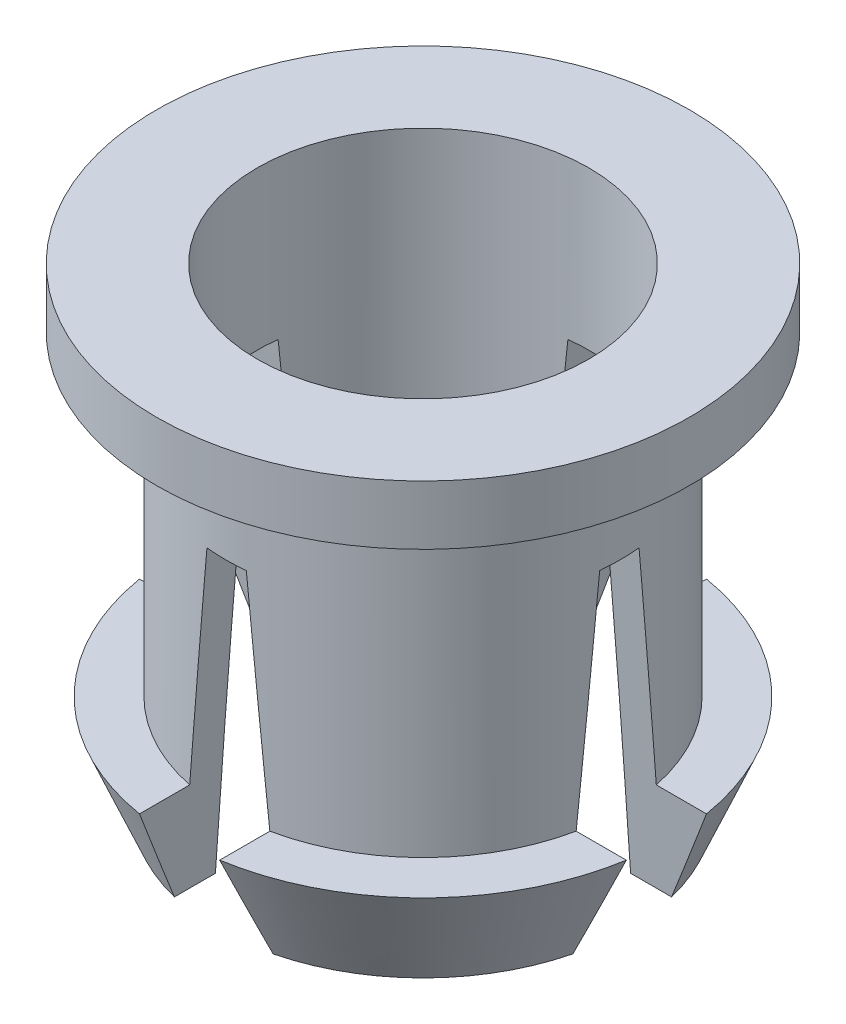
SolidWorks part; units mm, degrees
material "ABS"
ref_plane "Front Plane" through (0, 0, 0) normal (0, 0, 1) x (1, 0, 0)
ref_plane "Top Plane" through (0, 0, 0) normal (0, 1, 0) x (1, 0, 0)
ref_plane "Right Plane" through (0, 0, 0) normal (1, 0, 0) x (0, 0, -1)
sketch "Sketch1" plane through (0, 0, 0) normal (0, 0, 1) x (1, 0, 0)
  line L0 (0, 3) -> (0, -3) construction
  line L1 (2.1, 3) -> (2.1, -3)
  line L2 (2.1, -3) -> (2.6, -3)
  line L3 (2.6, -3) -> (3.125, -1.75)
  line L4 (3.125, -1.75) -> (2.5, -1.75)
  line L5 (2.5, -1.75) -> (2.5, 2.25)
  line L6 (2.5, 2.25) -> (3.375, 2.25)
  line L7 (3.375, 2.25) -> (3.375, 3)
  line L8 (3.375, 3) -> (2.1, 3)
  dimension "D1" = 6
  dimension "D2" = 4.2
  dimension "D3" = 0.5
  dimension "D4" = 5
  dimension "D5" = 6.75
  dimension "D6" = 0.75
  dimension "D7" = 1.25
  dimension "D8" = 6.25
revolve "Revolve1" add sketch "Sketch1" angle 360 about L0
sketch "Sketch2" plane through (0, 0, 0) normal (0, 0, 1) x (1, 0, 0)
  line L0 (-0.2495, 1) -> (0.2495, 1)
  line L1 (0.2495, 1) -> (0.625, -3)
  line L2 (-2.6, -3) -> (2.6, -3) construction
  line L3 (0.625, -3) -> (-0.625, -3)
  line L4 (-0.625, -3) -> (-0.2495, 1)
  point P5 (0, 1)
  dimension "D1" = 4
  dimension "D2" = 1.25
extrude "Cut-Extrude1" cut sketch "Sketch2" against normal through all and the other way through all
pattern_circular "CirPattern1" count 4 over 360 about axis through (0, 3, 0) along (0, 1, 0) of "Cut-Extrude1"
